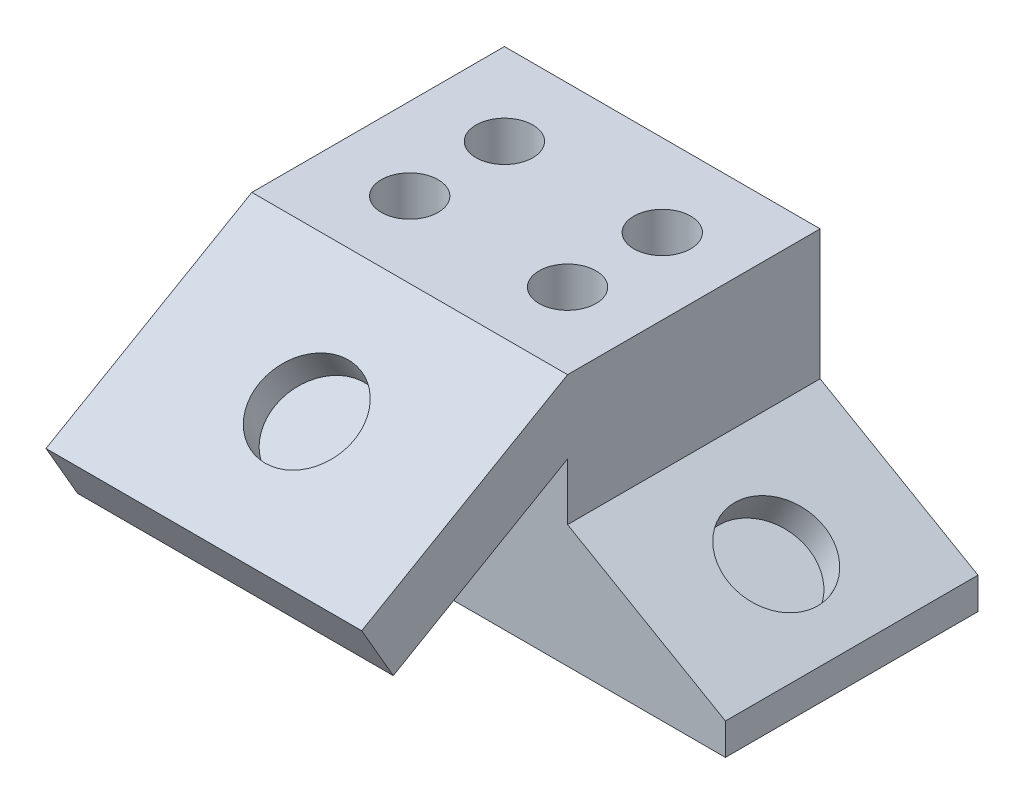
SolidWorks part; units mm, degrees
material "AISI 1020"
ref_plane "Front Plane" through (0, 0, 0) normal (0, 0, 1) x (1, 0, 0)
ref_plane "Top Plane" through (0, 0, 0) normal (0, 1, 0) x (1, 0, 0)
ref_plane "Right Plane" through (0, 0, 0) normal (1, 0, 0) x (0, 0, -1)
sketch "Sketch1" plane through (0, 0, 0) normal (0, 1, 0) x (1, 0, 0)
  line L1 (31.75, -25.4) -> (-31.75, -25.4)
  line L2 (31.75, -25.4) -> (31.75, 25.4)
  line L3 (31.75, 25.4) -> (-31.75, 25.4)
  line L4 (-31.75, -25.4) -> (-31.75, 25.4)
  line L5 (31.75, -25.4) -> (-31.75, 25.4) construction
  line L6 (31.75, 25.4) -> (-31.75, -25.4) construction
  point P0 (0, 0)
  dimension "D1" = 63.5
  dimension "D2" = 50.8
extrude "Boss-Extrude1" add sketch "Sketch1" along normal blind 50.8
sketch "Sketch2" plane through (0, 0, 25.4) normal (0, 0, 1) x (1, 0, 0)
  line L0 (31.75, 50.8) -> (31.75, 0) construction
  line L1 (31.75, 24.6809) -> (63.5, 6.35)
  line L2 (63.5, 6.35) -> (63.5, 0)
  line L3 (63.5, 0) -> (31.75, 0)
  line L4 (31.75, 24.6809) -> (31.75, 0)
  line L5 (-31.75, 0) -> (31.75, 0) construction
  line L6 (-31.75, 0) -> (31.75, 0)
  point P9 (31.75, 21.6372)
  line M7 (31.75, 0) -> (31.75, 50.8)
  dimension "D1" = 95.25
  dimension "D2" = 60
  dimension "D3" = 6.35
extrude "Boss-Extrude2" add sketch "Sketch2" against normal blind 50.8 contours L3 L2 L1 M7
sketch "Sketch3" plane through (18.6246, 32.2588, 0) normal (0.5, 0.866, 0) x (0.866, -0.5, 0)
  line L4 (53.3394, 25.4) -> (53.3394, -25.4)
  line L5 (16.6777, -25.4) -> (53.3394, -25.4)
  line L6 (16.6777, 25.4) -> (16.6777, -25.4)
  line L7 (16.6777, 25.4) -> (53.3394, 25.4)
  line L8 (35.0086, 25.4) -> (35.0086, -25.4) construction
  line L9 (16.6777, 0) -> (53.3394, 0) construction
  circle A0 centre (34.2894, 0) radius 9.652
  point P10 (0, 0)
  dimension "D1" = 19.05
  dimension "D2" = 19.304
  dimension "D3" = 25.4
  dimension "D4" = 50.8
extrude "Cut-Extrude2" cut sketch "Sketch3" against normal blind 6.35 contours A0
sketch "Sketch5" plane through (31.75, 0, 0) normal (1, 0, 0) x (0, 0, -1)
  line L0 (-25.4, 50.8) -> (-66.802, 26.8965)
  line L1 (-66.802, 26.8965) -> (-60.452, 15.898)
  line L2 (-60.452, 15.898) -> (-25.4, 36.1353)
  line L3 (-25.4, 50.8) -> (-25.4, 24.6809) construction
  line L4 (-25.4, 36.1353) -> (-25.4, 50.8)
  line L5 (-25.4, 50.8) -> (25.4, 50.8) construction
  dimension "D1" = 12.7
  dimension "D2" = 41.402
  dimension "D3" = 30
extrude "Boss-Extrude3" add sketch "Sketch5" against normal through all
sketch "Sketch6" plane through (0, 49.0985, 28.347) normal (0, 0.866, 0.5) x (1, 0, 0)
  line L0 (-31.75, -44.404) -> (31.75, -44.404) construction
  line L1 (31.75, 3.403) -> (31.75, -44.404) construction
  line L2 (-31.75, 3.403) -> (31.75, 3.403) construction
  line L3 (-31.75, 3.403) -> (-31.75, -44.404) construction
  line L4 (-31.75, -44.404) -> (31.75, -44.404)
  line L5 (31.75, 3.403) -> (31.75, -44.404)
  line L6 (-31.75, 3.403) -> (31.75, 3.403)
  line L7 (-31.75, 3.403) -> (-31.75, -44.404)
  line L8 (0, 52.1576) -> (0, -73.0863) construction
  line L9 (-31.75, -20.5005) -> (31.75, -20.5005) construction
  circle A0 centre (0, -20.5005) radius 9.652
  dimension "D1" = 19.304
extrude "Cut-Extrude4" cut sketch "Sketch6" against normal blind 6.35 contours A0
sketch "Sketch7" plane through (0, 50.8, 0) normal (0, 1, 0) x (1, 0, 0)
  line L0 (0, 46.6867) -> (0, -80.6656) construction
  line L1 (-54.6443, 8.89) -> (70.3883, 8.89) construction
  line L2 (-54.6443, -10.16) -> (72.244, -10.16) construction
  line L5 (-52.7885, 0) -> (72.244, 0) construction
  line L7 (-31.75, 25.4) -> (-31.75, -25.4) construction
  line L8 (-31.75, -25.4) -> (31.75, -25.4) construction
  circle A0 centre (-15.24, -10.16) radius 5.715
  circle A1 centre (-15.24, 8.89) radius 5.715
  circle A2 centre (16.51, -10.16) radius 5.715
  circle A3 centre (16.51, 8.89) radius 5.715
  point P7 (0, 0)
  point P8 (0, 0)
  point P17 (-15.875, 8.89)
  point P18 (0, 0)
  point P19 (0, 0)
  point P20 (0, 0)
  point P21 (0, 0)
  point P26 (0, 0)
  point P29 (0, 0)
  point P31 (-46.8048, 1.276)
  point P33 (0, 0)
  dimension "D3" = 19.05
  dimension "D4" = 16.51
  dimension "D6" = 11.43
  dimension "D1" = 31.75
  dimension "D2" = 31.75
  dimension "D5" = 15.24
extrude "Cut-Extrude6" cut sketch "Sketch7" against normal blind 12.7 contours A1 | A3 | A2 | A0
